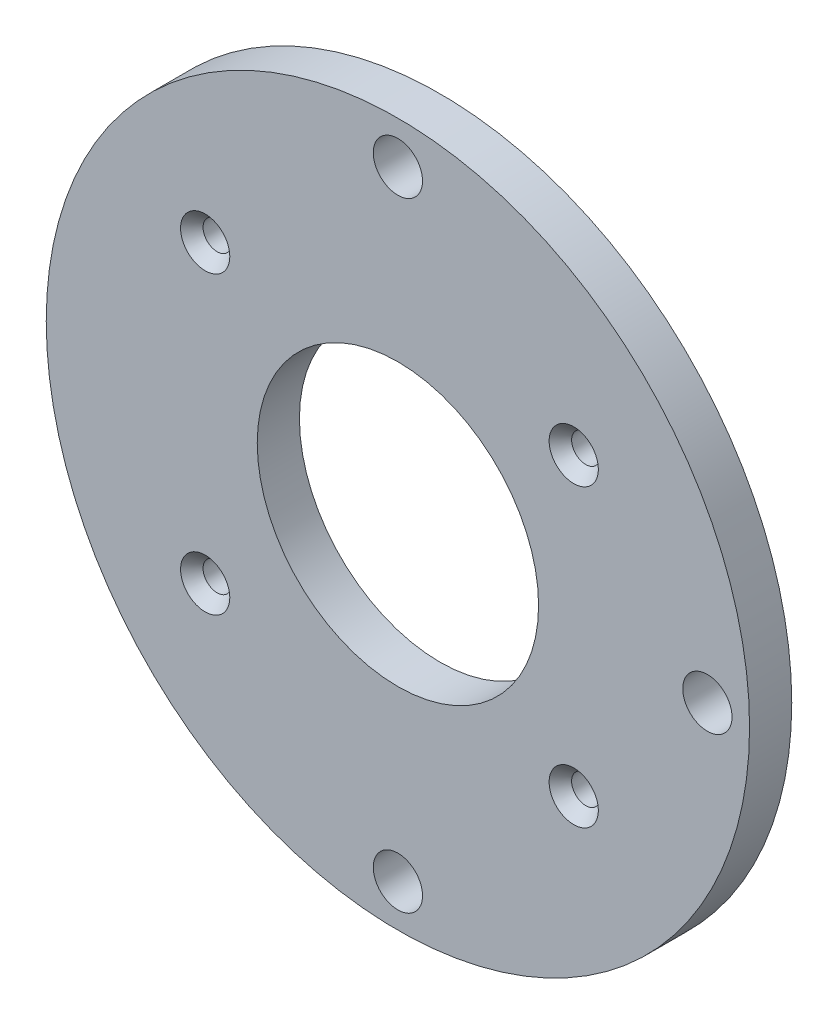
SolidWorks part; units mm, degrees
ref_plane "Спереди" through (0, 0, 0) normal (0, 0, 1) x (1, 0, 0)
ref_plane "Сверху" through (0, 0, 0) normal (0, 1, 0) x (1, 0, 0)
ref_plane "Справа" through (0, 0, 0) normal (1, 0, 0) x (0, 0, -1)
sketch "Эскиз1" plane through (0, 0, 0) normal (0, 1, 0) x (1, 0, 0)
  line L0 (25, 0) -> (0, 0)
  line L1 (0, 0) -> (0, -3)
  line L2 (0, -3) -> (25, -3)
  line L3 (25, -3) -> (25, 0)
  line L4 (0, 0) -> (0, -3) construction
revolve "Повернуть1" add sketch "Эскиз1" angle 360 about L4
hole_wizard "Отверстие1" positions "Эскиз3" profile "Эскиз2" legacy end condition through all
sketch "Эскиз3" plane through (0, 0, 3) normal (0, 0, 1) x (1, 0, 0)
  circle A0 centre (0, 0) radius 25 construction
  point P0 (-13.7, -10.5)
  dimension "D1" = 10.5
  dimension "D2" = 13.7
sketch "Эскиз2" plane through (-13.7, -10.5, 3) normal (1, 0, 0) x (0, -1, 0)
  line L0 (0, 0) -> (0, 3)
  line L1 (0, 3) -> (1.0065, 3)
  line L2 (1.0065, 3) -> (1.0065, 0)
  line L3 (1.0065, 0) -> (0, 0)
  line L4 (0, 110) -> (0, -10) construction
  dimension "Диаметр" = 2.013
  dimension "Глубина" = 3
hole_wizard "Отверстие2" positions "Эскиз5" profile "Эскиз4" legacy
sketch "Эскиз5" plane through (0, 0, 3) normal (0, 0, 1) x (1, 0, 0)
  circle A0 centre (0, 0) radius 25 construction
  point P0 (12.5, 10.5)
  dimension "D1" = 10.5
  dimension "D2" = 12.5
sketch "Эскиз4" plane through (12.5, 10.5, 3) normal (1, 0, 0) x (0, -1, 0)
  line L0 (0, 0) -> (0, 3)
  line L1 (0, 3) -> (1.0065, 3)
  line L2 (1.0065, 3) -> (1.0065, 0)
  line L3 (1.0065, 0) -> (0, 0)
  line L4 (0, 110) -> (0, -10) construction
  dimension "Диаметр" = 2.013
  dimension "Глубина" = 3
hole_wizard "Отверстие3" positions "Эскиз7" profile "Эскиз6" legacy
sketch "Эскиз7" plane through (0, 0, 3) normal (0, 0, 1) x (1, 0, 0)
  circle A1 centre (12.5, 10.5) radius 1.0065 construction
  circle A2 centre (-13.7, -10.5) radius 1.0065 construction
  point P0 (-13.7, 10.5)
  dimension "D1" = 26.2
  dimension "D2" = 21
sketch "Эскиз6" plane through (-13.7, 10.5, 3) normal (1, 0, 0) x (0, -1, 0)
  line L0 (0, 0) -> (0, 3)
  line L1 (0, 3) -> (1.0065, 3)
  line L2 (1.0065, 3) -> (1.0065, 0)
  line L3 (1.0065, 0) -> (0, 0)
  line L4 (0, 110) -> (0, -10) construction
  dimension "Диаметр" = 2.013
  dimension "Глубина" = 3
hole_wizard "Отверстие4" positions "Эскиз9" profile "Эскиз8" legacy
sketch "Эскиз9" plane through (0, 0, 3) normal (0, 0, 1) x (1, 0, 0)
  circle A0 centre (-13.7, -10.5) radius 1.0065 construction
  circle A1 centre (12.5, 10.5) radius 1.0065 construction
  point P0 (12.5, -10.5)
  dimension "D1" = 26.2
  dimension "D2" = 21
sketch "Эскиз8" plane through (12.5, -10.5, 3) normal (1, 0, 0) x (0, -1, 0)
  line L0 (0, 0) -> (0, 3)
  line L1 (0, 3) -> (1.0065, 3)
  line L2 (1.0065, 3) -> (1.0065, 0)
  line L3 (1.0065, 0) -> (0, 0)
  line L4 (0, 110) -> (0, -10) construction
  dimension "Диаметр" = 2.013
  dimension "Глубина" = 3
hole_wizard "Отверстие5" positions "Эскиз11" profile "Эскиз10" legacy
sketch "Эскиз11" plane through (0, 0, 3) normal (0, 0, 1) x (1, 0, 0)
  point P0 (0, -22)
  dimension "D1" = 22
sketch "Эскиз10" plane through (0, -22, 3) normal (1, 0, 0) x (0, -1, 0)
  line L0 (0, 0) -> (0, 3)
  line L1 (0, 3) -> (1.75, 3)
  line L2 (1.75, 3) -> (1.75, 0)
  line L3 (1.75, 0) -> (0, 0)
  line L4 (0, 110) -> (0, -10) construction
  dimension "Диаметр" = 3.5
  dimension "Глубина" = 3
hole_wizard "Отверстие6" positions "Эскиз13" profile "Эскиз12" legacy
sketch "Эскиз13" plane through (0, 0, 3) normal (0, 0, 1) x (1, 0, 0)
  point P0 (0, 22)
  dimension "D1" = 22
sketch "Эскиз12" plane through (0, 22, 3) normal (1, 0, 0) x (0, -1, 0)
  line L0 (0, 0) -> (0, 3)
  line L1 (0, 3) -> (1.75, 3)
  line L2 (1.75, 3) -> (1.75, 0)
  line L3 (1.75, 0) -> (0, 0)
  line L4 (0, 110) -> (0, -10) construction
  dimension "Диаметр" = 3.5
  dimension "Глубина" = 3
hole_wizard "Отверстие7" positions "Эскиз15" profile "Эскиз14" legacy
sketch "Эскиз15" plane through (0, 0, 3) normal (0, 0, 1) x (1, 0, 0)
  circle A0 centre (0, 0) radius 25 construction
  point P0 (0, 0)
sketch "Эскиз14" plane through (0, 0, 3) normal (1, 0, 0) x (0, -1, 0)
  line L0 (0, 0) -> (0, 3)
  line L1 (0, 3) -> (10, 3)
  line L2 (10, 3) -> (10, 0)
  line L3 (10, 0) -> (0, 0)
  line L4 (0, 110) -> (0, -10) construction
  dimension "Диаметр" = 20
  dimension "Глубина" = 3
hole_wizard "Отверстие8" positions "Эскиз17" profile "Эскиз16" legacy
sketch "Эскиз17" plane through (0, 0, 3) normal (0, 0, 1) x (1, 0, 0)
  circle A0 centre (0, 0) radius 25 construction
  point P0 (22, 0)
  dimension "D1" = 22
sketch "Эскиз16" plane through (22, 0, 3) normal (1, 0, 0) x (0, -1, 0)
  line L0 (0, 0) -> (0, 3)
  line L1 (0, 3) -> (1.75, 3)
  line L2 (1.75, 3) -> (1.75, 0)
  line L3 (1.75, 0) -> (0, 0)
  line L4 (0, 110) -> (0, -10) construction
  dimension "Диаметр" = 3.5
  dimension "Глубина" = 3
chamfer "Фаска1" distance 0.7435 angle 49 1 edges at (-12.6935, 10.5, 3)
chamfer "Фаска2" distance 0.7435 angle 49 1 edges at (13.5065, -10.5, 3)
chamfer "Фаска3" distance 0.7435 angle 49 1 edges at (13.5065, 10.5, 3)
chamfer "Фаска4" distance 0.7435 angle 49 1 edges at (-12.6935, -10.5, 3)
